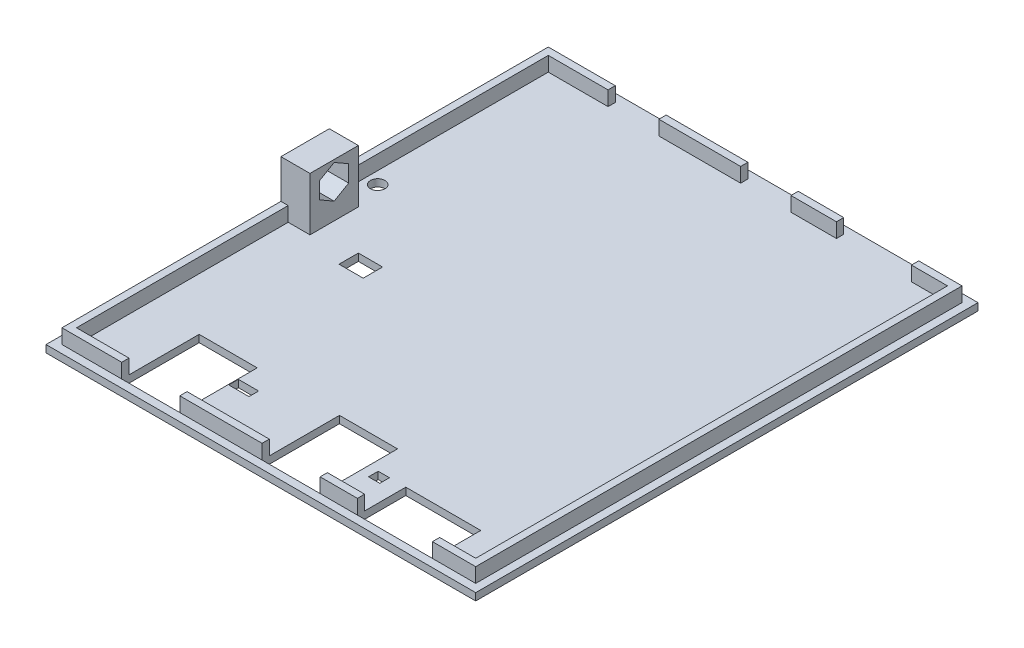
SolidWorks part; units mm, degrees
ref_plane "前视基准面" through (0, 0, 0) normal (0, 0, 1) x (1, 0, 0)
ref_plane "上视基准面" through (0, 0, 0) normal (0, 1, 0) x (1, 0, 0)
ref_plane "右视基准面" through (0, 0, 0) normal (1, 0, 0) x (0, 0, -1)
sketch "草图1" plane through (0, 0, 0) normal (0, 1, 0) x (1, 0, 0)
  line L0 (44.4, 51.9) -> (-44.4, 51.9)
  line L1 (42.5, -50) -> (-42.5, -50) construction
  line L2 (42.5, -50) -> (42.5, 50) construction
  line L3 (42.5, 50) -> (-42.5, 50) construction
  line L4 (-42.5, -50) -> (-42.5, 50) construction
  line L5 (42.5, -50) -> (-42.5, 50) construction
  line L6 (42.5, 50) -> (-42.5, -50) construction
  line L7 (-44.4, -51.9) -> (-44.4, 51.9)
  line L8 (44.4, -51.9) -> (-44.4, -51.9)
  line L9 (44.4, -51.9) -> (44.4, 51.9)
  line L10 (42.75, 50.25) -> (-42.75, 50.25) construction
  line L11 (-42.75, -50.25) -> (-42.75, 50.25) construction
  line L12 (42.75, -50.25) -> (-42.75, -50.25) construction
  line L13 (42.75, -50.25) -> (42.75, 50.25) construction
  point P0 (0, 0)
  dimension "D1" = 85
  dimension "D2" = 100
  dimension "D3" = 1.9
  dimension "D4" = 1.65
extrude "凸台-拉伸1" add sketch "草图1" along normal blind 1.5
sketch "草图2" plane through (0, 1.5, 0) normal (0, 1, 0) x (1, 0, 0)
  line L0 (42.75, -50.25) -> (-42.75, -50.25) construction
  line L1 (42.75, -50.25) -> (42.75, 50.25) construction
  line L2 (-42.75, -50.25) -> (-42.75, 50.25) construction
  line L3 (42.75, 50.25) -> (-42.75, 50.25) construction
  line L4 (42.75, 50.25) -> (-42.75, 50.25)
  line L5 (-42.75, -50.25) -> (-42.75, 50.25)
  line L6 (42.75, -50.25) -> (42.75, 50.25)
  line L7 (42.75, -50.25) -> (-42.75, -50.25)
  line L8 (41.25, 48.75) -> (-41.25, 48.75)
  line L9 (-41.25, -48.75) -> (-41.25, 48.75)
  line L10 (41.25, -48.75) -> (-41.25, -48.75)
  line L11 (41.25, -48.75) -> (41.25, 48.75)
  dimension "D1" = 1.5
extrude "凸台-拉伸2" add sketch "草图2" along normal blind 3
sketch "草图3" plane through (-42.75, 0, 0) normal (-1, 0, 0) x (0, 0, 1)
  line L0 (0, 0) -> (0, 17.4499) construction
  line L1 (-50.25, 4.5) -> (50.25, 4.5) construction
  line L2 (5, 12.5) -> (-5, 12.5)
  line L3 (5, 12.5) -> (5, 4.5)
  line L4 (5, 4.5) -> (-5, 4.5) construction
  line L5 (-5, 12.5) -> (-5, 4.5)
  line L6 (5, 12.5) -> (-5, 4.5) construction
  line L7 (5, 4.5) -> (-5, 12.5) construction
  line L9 (-50.25, 1.5) -> (50.25, 1.5) construction
  line L10 (0, 11.9641) -> (-3, 10.2321)
  line L11 (-3, 10.2321) -> (-3, 6.7679)
  line L12 (-3, 6.7679) -> (0, 5.0359)
  line L13 (0, 5.0359) -> (3, 6.7679)
  line L14 (3, 6.7679) -> (3, 10.2321)
  line L15 (3, 10.2321) -> (0, 11.9641)
  line L16 (-5, 4.5) -> (-5, 1.5)
  line L17 (-5, 1.5) -> (5, 1.5)
  line L18 (-51.9, 1.5) -> (51.9, 1.5) construction
  line L19 (5, 1.5) -> (5, 4.5)
  circle A0 centre (0, 8.5) radius 3 construction
  point P2 (0, 8.5)
  dimension "D3" = 6
  dimension "D1" = 10
  dimension "D2" = 7
extrude "凸台-拉伸3" add sketch "草图3" against normal blind 6
sketch "草图6" plane through (0, 0, -50.25) normal (0, 0, -1) x (-1, 0, 0)
  line L0 (28.9, 1.5) -> (28.9, 7.5)
  line L1 (-44.4, 1.5) -> (44.4, 1.5) construction
  line L2 (28.9, 7.5) -> (18.4, 7.5)
  line L3 (18.4, 7.5) -> (18.4, 1.5)
  line L4 (18.4, 1.5) -> (28.9, 1.5)
  line L5 (44.4, 1.5) -> (44.4, 0) construction
  line L6 (-44.4, 1.5) -> (-44.4, 0) construction
  line L7 (-33.8, 1.5) -> (-18.3, 1.5)
  line L8 (-33.8, 1.5) -> (-33.8, 7.5)
  line L9 (-33.8, 7.5) -> (-18.3, 7.5)
  line L10 (-18.3, 1.5) -> (-18.3, 7.5)
  line L11 (-42.75, 1.5) -> (42.75, 1.5) construction
  line L13 (-8.9, 1.5) -> (1.5, 1.5)
  line L14 (-8.9, 1.5) -> (-8.9, 7.5)
  line L15 (-8.9, 7.5) -> (1.5, 7.5)
  line L16 (1.5, 1.5) -> (1.5, 7.5)
  point P4 (44.4, 0.75)
  point P9 (44.4, 0.75)
  point P16 (-44.4, 0.75)
  dimension "D1" = 15.5
  dimension "D2" = 26
  dimension "D3" = 6
  dimension "D4" = 15.5
  dimension "D5" = 6
  dimension "D6" = 10.6
  dimension "D7" = 0
  dimension "D8" = 10.4
  dimension "D9" = 9.4
  dimension "D10" = 6
  dimension "D11" = 0
extrude "切除-拉伸2" cut sketch "草图6" against normal blind 1.5
sketch "草图7" plane through (0, 0, 0) normal (0, 1, 0) x (1, 0, 0)
  line L1 (33.8, -40.25) -> (18.3, -40.25)
  line L2 (33.8, -40.25) -> (33.8, -50.25)
  line L3 (33.8, -50.25) -> (18.3, -50.25)
  line L4 (18.3, -40.25) -> (18.3, -50.25)
  line L5 (18.3, 48.75) -> (18.3, 50.25) construction
  line L7 (10.6, -34.25) -> (-1.4, -34.25)
  line L8 (10.6, -34.25) -> (10.6, -50.25)
  line L9 (10.6, -50.25) -> (-1.4, -50.25)
  line L10 (-1.4, -34.25) -> (-1.4, -50.25)
  line L11 (-44.4, -51.9) -> (-44.4, 51.9) construction
  line L12 (-18.4, -50.25) -> (-30.4, -50.25)
  line L13 (-18.4, -50.25) -> (-18.4, -34.25)
  line L14 (-18.4, -34.25) -> (-30.4, -34.25)
  line L15 (-30.4, -50.25) -> (-30.4, -34.25)
  line L16 (42.5, 50) -> (-42.5, 50) construction
  line L17 (12.6, -42.25) -> (14.9256, -42.25)
  line L19 (-18.3, -40.25) -> (-14.111, -40.25)
  line L20 (-18.3, -40.25) -> (-18.3, -38.25)
  line L21 (12.6, -42.25) -> (12.6, -40.25)
  line L22 (12.6, -40.25) -> (14.9256, -40.25)
  line L23 (14.9256, -42.25) -> (14.9256, -40.25)
  line L25 (-28.5, -3.25) -> (-23.5, -3.25)
  line L26 (-28.5, -3.25) -> (-28.5, -7.25)
  line L27 (-28.5, -7.25) -> (-23.5, -7.25)
  line L28 (-23.5, -3.25) -> (-23.5, -7.25)
  line L29 (-42.5, -50) -> (-42.5, 50) construction
  line L30 (-42.75, -50.25) -> (-42.75, 50.25) construction
  line L33 (42.75, -50.25) -> (-42.75, -50.25) construction
  line L34 (-18.3, -38.25) -> (-14.111, -38.25)
  line L35 (-14.111, -40.25) -> (-14.111, -38.25)
  circle A0 centre (-38.75, 11) radius 1.5
  point P26 (-16.2055, -40.25)
  dimension "D22" = 4
  dimension "D1" = 10
  dimension "D3" = 15.5
  dimension "D4" = 0
  dimension "D5" = 7.7
  dimension "D6" = 16
  dimension "D7" = 16
  dimension "D8" = 12
  dimension "D9" = 10
  dimension "D10" = 16
  dimension "D11" = 0
  dimension "D12" = 12
  dimension "D13" = 0.1
  dimension "D14" = 10
  dimension "D15" = 39
  dimension "D16" = 2
  dimension "D17" = 14
  dimension "D18" = 2
  dimension "D19" = 43
  dimension "D20" = 14
  dimension "D21" = 5
  dimension "D23" = 4
  dimension "D24" = 8
  dimension "D25" = 2
extrude "切除-拉伸5" cut sketch "草图7" along normal blind 10
